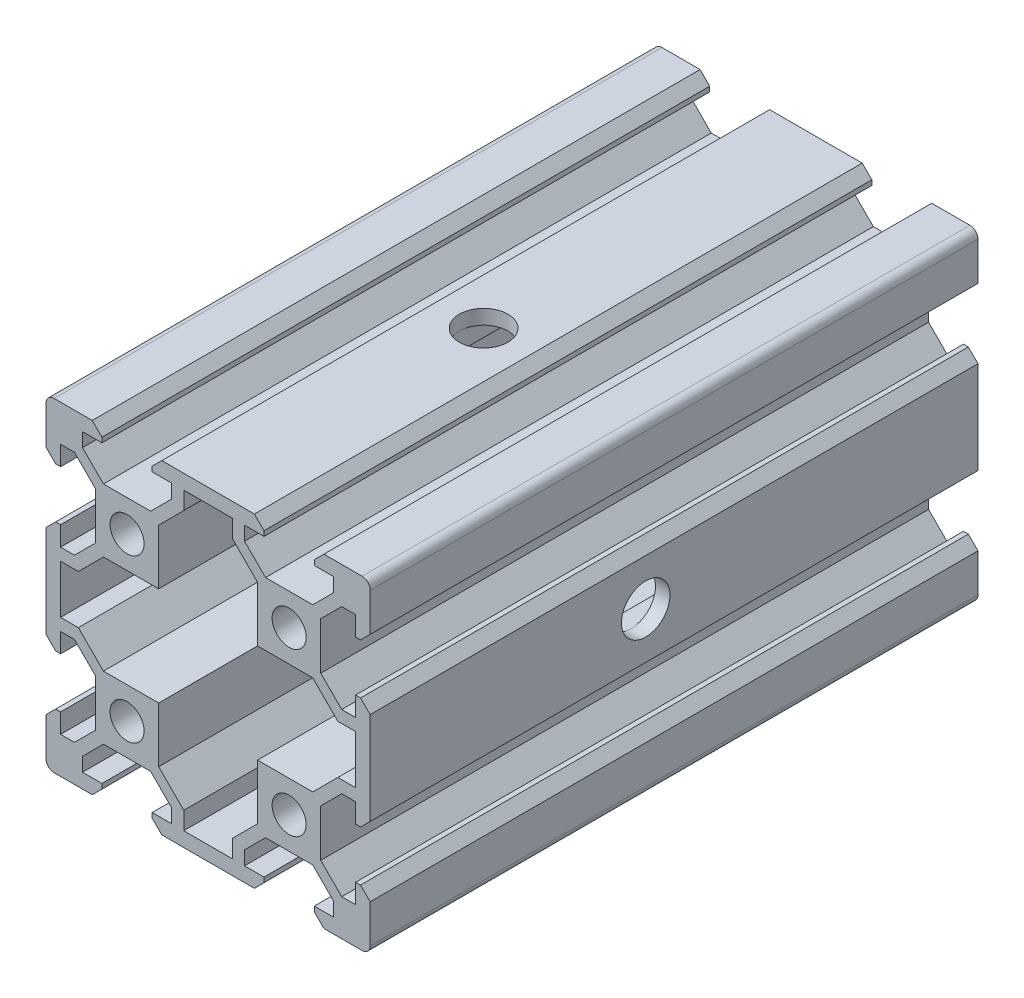
SolidWorks part; units mm, degrees
ref_plane "Front" through (0, 0, 0) normal (0, 0, 1) x (1, 0, 0)
ref_plane "Top" through (0, 0, 0) normal (0, 1, 0) x (1, 0, 0)
ref_plane "Right" through (0, 0, 0) normal (1, 0, 0) x (0, 0, -1)
sketch "草图1" plane through (0, 0, 0) normal (0, 0, 1) x (1, 0, 0)
  line L0 (0, 20) -> (0, -20) construction
  line L1 (-20, -20) -> (20, -20) construction
  line L2 (-20, -20) -> (-20, 20) construction
  line L3 (-20, 20) -> (20, 20) construction
  line L4 (20, -20) -> (20, 20) construction
  line L5 (-20, -20) -> (20, 20) construction
  line L6 (-20, 20) -> (-10, 10) construction
  line L7 (-20, 0) -> (20, 0) construction
  line L8 (5.71, 20) -> (-5.71, 20)
  line L9 (-5.71, 20) -> (-6.9, 18.81)
  line L10 (-6.9, 18.81) -> (-6.9, 18.2)
  line L11 (-6.9, 18.2) -> (-4.5, 18.2)
  line L12 (-4.5, 18.2) -> (-4.5, 16.4899)
  line L13 (-4.5, 16.4899) -> (-7.0899, 13.9)
  line L14 (-7.0899, 13.9) -> (-12.9101, 13.9)
  line L15 (-6.1, 6.1) -> (-6.1, 12.9101)
  line L16 (-6.1, 12.9101) -> (-3, 16.0101)
  line L17 (-3, 16.0101) -> (-3, 18.2)
  line L18 (-3, 18.2) -> (3, 18.2)
  line L19 (-20, 20) -> (-14.29, 20)
  line L20 (-14.29, 20) -> (-13.1, 18.81)
  line L21 (-13.1, 18.81) -> (-13.1, 18.2)
  line L22 (-13.1, 18.2) -> (-15.5, 18.2)
  line L23 (-15.5, 18.2) -> (-15.5, 16.4899)
  line L24 (-15.5, 16.4899) -> (-12.9101, 13.9)
  line L25 (-10, 10) -> (0, 20) construction
  line L26 (-10, 10) -> (-10, 20) construction
  line L27 (-13.9, 6.1) -> (-6.1, 6.1) construction
  line L28 (-13.9, 6.1) -> (-13.9, 13.9) construction
  line L29 (-13.9, 13.9) -> (-6.1, 13.9) construction
  line L30 (-6.1, 6.1) -> (-6.1, 13.9) construction
  line L31 (-13.9, 6.1) -> (-6.1, 13.9) construction
  line L32 (-13.9, 13.9) -> (-10, 10) construction
  line L35 (-10, 10) -> (-6.1, 6.1) construction
  line L37 (-10, 10) -> (20, -20) construction
  line L38 (-16.0101, -3) -> (-18.2, -3)
  line L39 (-20, 20) -> (-20, 14.29)
  line L40 (-20, 14.29) -> (-18.81, 13.1)
  line L41 (-18.81, 13.1) -> (-18.2, 13.1)
  line L42 (-18.2, 13.1) -> (-18.2, 15.5)
  line L43 (-18.2, 15.5) -> (-16.4899, 15.5)
  line L44 (-16.4899, 15.5) -> (-13.9, 12.9101)
  line L45 (-13.9, 7.0899) -> (-13.9, 12.9101)
  line L46 (-16.4899, 4.5) -> (-13.9, 7.0899)
  line L47 (-18.2, 4.5) -> (-16.4899, 4.5)
  line L48 (-18.2, 6.9) -> (-18.2, 4.5)
  line L49 (-18.81, 6.9) -> (-18.2, 6.9)
  line L50 (-20, 5.71) -> (-18.81, 6.9)
  line L51 (-20, -5.71) -> (-20, 5.71)
  line L53 (-18.2, 3) -> (-18.2, -3)
  line L54 (-16.0101, 3) -> (-18.2, 3)
  line L55 (-12.9101, 6.1) -> (-16.0101, 3)
  line L56 (-6.1, 6.1) -> (-12.9101, 6.1)
  line L57 (-12.9101, -6.1) -> (-16.0101, -3)
  line L58 (-6.1, -6.1) -> (-12.9101, -6.1)
  line L59 (-6.1, -6.1) -> (-6.1, -12.9101)
  line L60 (-6.1, -12.9101) -> (-3, -16.0101)
  line L61 (-3, -16.0101) -> (-3, -18.2)
  line L62 (-3, -18.2) -> (3, -18.2)
  line L64 (5.71, -20) -> (-5.71, -20)
  line L65 (-5.71, -20) -> (-6.9, -18.81)
  line L66 (-6.9, -18.81) -> (-6.9, -18.2)
  line L67 (-6.9, -18.2) -> (-4.5, -18.2)
  line L68 (-4.5, -18.2) -> (-4.5, -16.4899)
  line L69 (-4.5, -16.4899) -> (-7.0899, -13.9)
  line L70 (-7.0899, -13.9) -> (-12.9101, -13.9)
  line L71 (-15.5, -16.4899) -> (-12.9101, -13.9)
  line L72 (-15.5, -18.2) -> (-15.5, -16.4899)
  line L73 (-13.1, -18.2) -> (-15.5, -18.2)
  line L74 (-13.1, -18.81) -> (-13.1, -18.2)
  line L75 (-14.29, -20) -> (-13.1, -18.81)
  line L76 (-20, -20) -> (-14.29, -20)
  line L77 (-20, -20) -> (-20, -14.29)
  line L78 (-20, -14.29) -> (-18.81, -13.1)
  line L79 (-18.81, -13.1) -> (-18.2, -13.1)
  line L80 (-18.2, -13.1) -> (-18.2, -15.5)
  line L81 (-18.2, -15.5) -> (-16.4899, -15.5)
  line L82 (-16.4899, -15.5) -> (-13.9, -12.9101)
  line L83 (-13.9, -7.0899) -> (-13.9, -12.9101)
  line L84 (-16.4899, -4.5) -> (-13.9, -7.0899)
  line L85 (-18.2, -4.5) -> (-16.4899, -4.5)
  line L86 (-18.2, -6.9) -> (-18.2, -4.5)
  line L87 (-18.81, -6.9) -> (-18.2, -6.9)
  line L88 (-20, -5.71) -> (-18.81, -6.9)
  line L89 (13.9, 13.9) -> (10, 10) construction
  line L90 (13.9, 6.1) -> (6.1, 13.9) construction
  line L91 (6.1, 6.1) -> (6.1, 13.9) construction
  line L92 (13.9, 13.9) -> (6.1, 13.9) construction
  line L93 (13.9, 6.1) -> (13.9, 13.9) construction
  line L94 (13.9, 6.1) -> (6.1, 6.1) construction
  line L95 (10, 10) -> (10, 20) construction
  line L96 (10, 10) -> (0, 20) construction
  line L97 (20, -5.71) -> (18.81, -6.9)
  line L98 (18.81, -6.9) -> (18.2, -6.9)
  line L99 (18.2, -6.9) -> (18.2, -4.5)
  line L100 (18.2, -4.5) -> (16.4899, -4.5)
  line L101 (16.4899, -4.5) -> (13.9, -7.0899)
  line L102 (13.9, -7.0899) -> (13.9, -12.9101)
  line L103 (16.4899, -15.5) -> (13.9, -12.9101)
  line L104 (18.2, -15.5) -> (16.4899, -15.5)
  line L105 (18.2, -13.1) -> (18.2, -15.5)
  line L106 (18.81, -13.1) -> (18.2, -13.1)
  line L107 (20, -14.29) -> (18.81, -13.1)
  line L108 (20, -20) -> (20, -14.29)
  line L109 (20, -20) -> (14.29, -20)
  line L110 (14.29, -20) -> (13.1, -18.81)
  line L111 (13.1, -18.81) -> (13.1, -18.2)
  line L112 (13.1, -18.2) -> (15.5, -18.2)
  line L113 (15.5, -18.2) -> (15.5, -16.4899)
  line L114 (15.5, -16.4899) -> (12.9101, -13.9)
  line L115 (7.0899, -13.9) -> (12.9101, -13.9)
  line L116 (4.5, -16.4899) -> (7.0899, -13.9)
  line L117 (4.5, -18.2) -> (4.5, -16.4899)
  line L118 (6.9, -18.2) -> (4.5, -18.2)
  line L119 (6.9, -18.81) -> (6.9, -18.2)
  line L120 (5.71, -20) -> (6.9, -18.81)
  line L121 (3, -16.0101) -> (3, -18.2)
  line L122 (6.1, -12.9101) -> (3, -16.0101)
  line L123 (6.1, -6.1) -> (6.1, -12.9101)
  line L124 (6.1, -6.1) -> (12.9101, -6.1)
  line L125 (12.9101, -6.1) -> (16.0101, -3)
  line L126 (6.1, 6.1) -> (12.9101, 6.1)
  line L127 (12.9101, 6.1) -> (16.0101, 3)
  line L128 (16.0101, 3) -> (18.2, 3)
  line L129 (18.2, 3) -> (18.2, -3)
  line L130 (20, -5.71) -> (20, 5.71)
  line L131 (20, 5.71) -> (18.81, 6.9)
  line L132 (18.81, 6.9) -> (18.2, 6.9)
  line L133 (18.2, 6.9) -> (18.2, 4.5)
  line L134 (18.2, 4.5) -> (16.4899, 4.5)
  line L135 (16.4899, 4.5) -> (13.9, 7.0899)
  line L136 (13.9, 7.0899) -> (13.9, 12.9101)
  line L137 (16.4899, 15.5) -> (13.9, 12.9101)
  line L138 (18.2, 15.5) -> (16.4899, 15.5)
  line L139 (18.2, 13.1) -> (18.2, 15.5)
  line L140 (18.81, 13.1) -> (18.2, 13.1)
  line L141 (20, 14.29) -> (18.81, 13.1)
  line L142 (20, 20) -> (20, 14.29)
  line L143 (16.0101, -3) -> (18.2, -3)
  line L144 (15.5, 16.4899) -> (12.9101, 13.9)
  line L145 (15.5, 18.2) -> (15.5, 16.4899)
  line L146 (13.1, 18.2) -> (15.5, 18.2)
  line L147 (13.1, 18.81) -> (13.1, 18.2)
  line L148 (14.29, 20) -> (13.1, 18.81)
  line L149 (20, 20) -> (14.29, 20)
  line L150 (3, 16.0101) -> (3, 18.2)
  line L151 (6.1, 12.9101) -> (3, 16.0101)
  line L152 (6.1, 6.1) -> (6.1, 12.9101)
  line L153 (7.0899, 13.9) -> (12.9101, 13.9)
  line L154 (4.5, 16.4899) -> (7.0899, 13.9)
  line L155 (4.5, 18.2) -> (4.5, 16.4899)
  line L156 (6.9, 18.2) -> (4.5, 18.2)
  line L157 (6.9, 18.81) -> (6.9, 18.2)
  line L158 (5.71, 20) -> (6.9, 18.81)
  circle A0 centre (-10, 10) radius 2.1
  circle A1 centre (-10, -10) radius 2.1
  circle A2 centre (10, -10) radius 2.1
  circle A3 centre (10, 10) radius 2.1
  point P0 (0, 0)
  point P59 (-18.2, 0)
  point P124 (0, -18.2)
  point P152 (0, 18.2)
  dimension "D10" = 4.2
  dimension "D1" = 40
  dimension "D2" = 6
  dimension "D3" = 1.8
  dimension "D4" = 45
  dimension "D5" = 4.5
  dimension "D6" = 45
  dimension "D7" = 6.2
  dimension "D8" = 0.61
  dimension "D9" = 1.4
  dimension "D12" = 7.8
  dimension "D13" = 1.5
  dimension "D14" = 1.4
  dimension "D15" = 7.8
extrude "凸台-拉伸1" add sketch "草图1" along normal blind 75
ref_plane "Ebene1" through (0, 0, 0) normal (-0.7071, -0.7071, 0) x (-0.7071, 0.7071, 0)
fillet "Verrundung1" radius 1 4 edges at (20, -20, 37.5) (-20, -20, 37.5) (-20, 20, 37.5) (20, 20, 37.5)
ref_plane "Plane1" through (0, 0, 0) normal (-0.7071, 0.7071, 0) x (0.7071, 0.7071, 0)
sketch "Sketch1" plane through (-20, 0, 0) normal (-1, 0, 0) x (0, 0, 1)
  line L1 (75, 5.71) -> (75, -5.71) construction
  circle A0 centre (41, 0) radius 3
  dimension "D1" = 6
  dimension "D2" = 34
extrude "Cut-Extrude1" cut sketch "Sketch1" against normal through all
mirror "Mirror1" about plane through (0, 0, 0) normal (-0.7071, -0.7071, 0) of "Cut-Extrude1"
